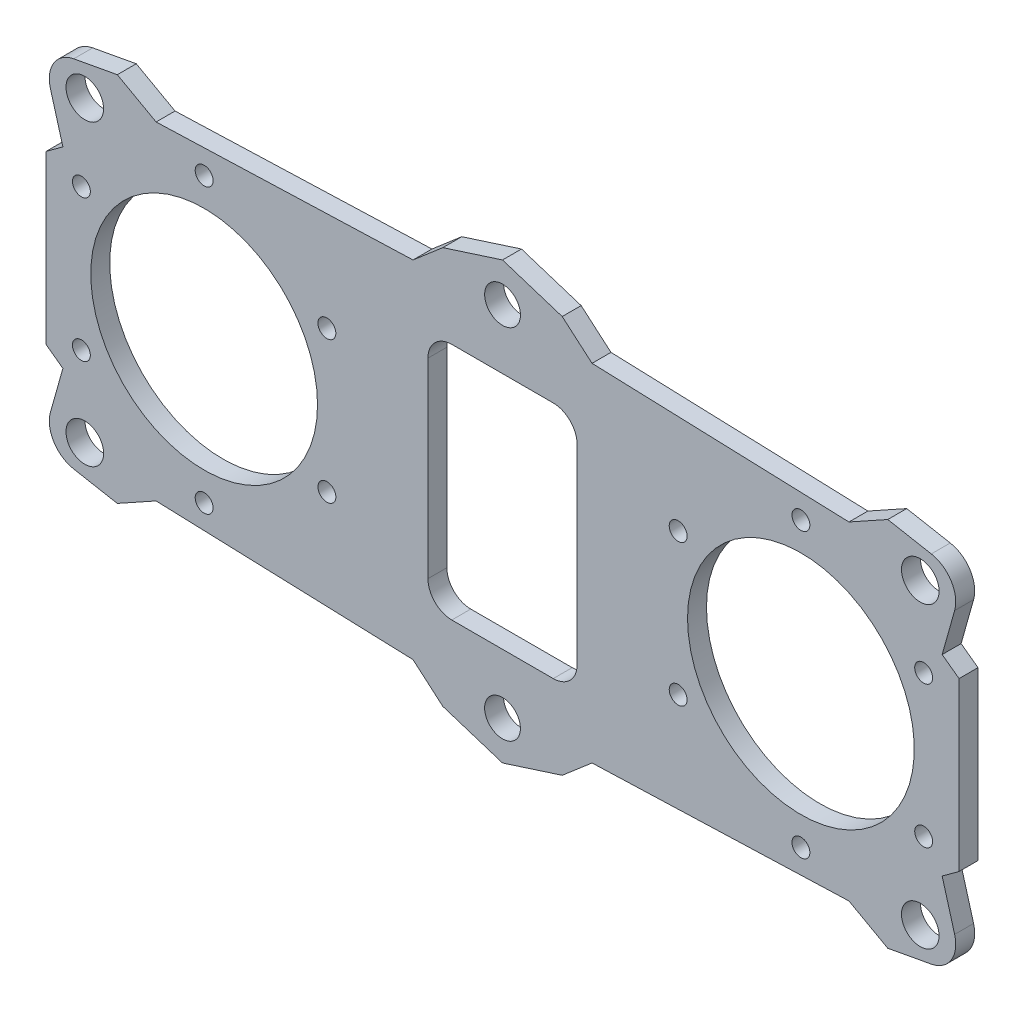
SolidWorks part; units mm, degrees
ref_plane "Front Plane" through (0, 0, 0) normal (0, 0, 1) x (1, 0, 0)
ref_plane "Top Plane" through (0, 0, 0) normal (0, 1, 0) x (1, 0, 0)
ref_plane "Right Plane" through (0, 0, 0) normal (1, 0, 0) x (0, 0, -1)
sketch "Sketch1" plane through (0, 0, 0) normal (0, 0, 1) x (1, 0, 0)
  line L0 (0, 36.5) -> (-10, 33.2896)
  line L1 (-10, 33.2896) -> (-15, 29)
  line L2 (-15, 29) -> (-58.05, 27.5)
  line L3 (-58.05, 27.5) -> (-76.5, 14)
  line L4 (-76.5, 14) -> (-76.5, -14)
  line L5 (-87.0431, 0) -> (20.0163, 0) construction
  line L6 (0, 32.2788) -> (0, 0) construction
  line L7 (76.5, 14) -> (76.5, -14)
  line L8 (58.05, 27.5) -> (76.5, 14)
  line L9 (15, 29) -> (58.05, 27.5)
  line L10 (10, 33.2896) -> (15, 29)
  line L11 (0, 36.5) -> (10, 33.2896)
  line L12 (0, -36.5) -> (10, -33.2896)
  line L13 (10, -33.2896) -> (15, -29)
  line L14 (15, -29) -> (58.05, -27.5)
  line L15 (58.05, -27.5) -> (76.5, -14)
  line L16 (-58.05, -27.5) -> (-76.5, -14)
  line L17 (-15, -29) -> (-58.05, -27.5)
  line L18 (-10, -33.2896) -> (-15, -29)
  line L19 (0, -36.5) -> (-10, -33.2896)
  circle A0 centre (0, 30) radius 3
  circle A1 centre (-50, 0) radius 19
  circle A2 centre (50, 0) radius 19
  circle A3 centre (0, -30) radius 3
  point P35 (76.5, 0)
  point P36 (-76.5, 0)
  dimension "D1" = 6
  dimension "D2" = 38
  dimension "D3" = 60
  dimension "D4" = 100
  dimension "D5" = 153
  dimension "D6" = 73
  dimension "D7" = 28
  dimension "D8" = 55
  dimension "D9" = 18.45
  dimension "D10" = 30
  dimension "D11" = 20
  dimension "D12" = 58
extrude "Boss-Extrude1" add sketch "Sketch1" along normal blind 3.175
sketch "Sketch2" plane through (0, 0, 3.175) normal (0, 0, 1) x (1, 0, 0)
  line L1 (8.5, 20) -> (-8.5, 20)
  line L2 (12.5, 16) -> (12.5, -16)
  line L3 (8.5, -20) -> (-8.5, -20)
  line L4 (-12.5, 16) -> (-12.5, -16)
  line L5 (12.5, 20) -> (-12.5, -20) construction
  line L6 (12.5, -20) -> (-12.5, 20) construction
  arc A1 (8.5, 20) -> (12.5, 16) centre (8.5, 16) cw
  arc A2 (12.5, -16) -> (8.5, -20) centre (8.5, -16) cw
  arc A3 (-8.5, -20) -> (-12.5, -16) centre (-8.5, -16) cw
  arc A4 (-8.5, 20) -> (-12.5, 16) centre (-8.5, 16) ccw
  point P0 (0, 0)
  dimension "D1" = 4
  dimension "D2" = 25
  dimension "D3" = 40
extrude "Cut-Extrude1" cut sketch "Sketch2" against normal through all
sketch "Sketch3" plane through (0, 0, 3.175) normal (0, 0, 1) x (1, 0, 0)
  line L0 (-58.05, 27.5) -> (-64.5519, 31.11)
  line L1 (-58.05, 27.5) -> (-76.5, 14) construction
  line L2 (-64.5519, 31.11) -> (-77.2451, 28.7738)
  line L3 (-77.2451, 28.7738) -> (-73.6694, 16.0712)
  line L4 (-73.6694, 16.0712) -> (-58.05, 27.5)
  line L5 (0, 0) -> (0, 46.5274) construction
  line L6 (73.6694, 16.0712) -> (58.05, 27.5)
  line L7 (77.2451, 28.7738) -> (73.6694, 16.0712)
  line L8 (64.5519, 31.11) -> (77.2451, 28.7738)
  line L9 (58.05, 27.5) -> (64.5519, 31.11)
  line L10 (0, 0) -> (-26.0239, 0) construction
  line L11 (58.05, -27.5) -> (64.5519, -31.11)
  line L12 (64.5519, -31.11) -> (77.2451, -28.7738)
  line L13 (77.2451, -28.7738) -> (73.6694, -16.0712)
  line L14 (73.6694, -16.0712) -> (58.05, -27.5)
  line L15 (-73.6694, -16.0712) -> (-58.05, -27.5)
  line L16 (-77.2451, -28.7738) -> (-73.6694, -16.0712)
  line L17 (-64.5519, -31.11) -> (-77.2451, -28.7738)
  line L18 (-58.05, -27.5) -> (-64.5519, -31.11)
  line L19 (-15, 29) -> (-58.05, 27.5) construction
  circle A0 centre (-70, 25) radius 3.15
  circle A1 centre (70, 25) radius 3.15
  circle A2 centre (-70, -25) radius 3.15
  circle A3 centre (70, -25) radius 3.15
  dimension "D1" = 6.3
  dimension "D2" = 70
  dimension "D3" = 25
extrude "Boss-Extrude2" add sketch "Sketch3" against normal up to surface (3.175 mm away) up to face at (0, 0, 0)
fillet "Fillet1" radius 5 4 edges at (-77.2451, 28.7738, 1.5875) (-77.2451, -28.7738, 1.5875) (77.2451, -28.7738, 1.5875) (77.2451, 28.7738, 1.5875)
sketch "Sketch4" plane through (0, 0, 3.175) normal (0, 0, 1) x (1, 0, 0)
  line L0 (0, 48.5627) -> (0, -47.8194) construction
  circle A0 centre (-50, 0) radius 23.75 construction
  circle A1 centre (-50, 23.75) radius 1.5
  circle A2 centre (-70.5681, 11.875) radius 1.5
  circle A3 centre (-70.5681, -11.875) radius 1.5
  circle A4 centre (-50, -23.75) radius 1.5
  circle A5 centre (-29.4319, -11.875) radius 1.5
  circle A6 centre (-29.4319, 11.875) radius 1.5
  circle A7 centre (29.4319, 11.875) radius 1.5
  circle A8 centre (29.4319, -11.875) radius 1.5
  circle A9 centre (50, -23.75) radius 1.5
  circle A10 centre (70.5681, -11.875) radius 1.5
  circle A11 centre (70.5681, 11.875) radius 1.5
  circle A12 centre (50, 23.75) radius 1.5
  point P21 (-50, 0)
  point P31 (50, 0)
  dimension "D1" = 47.5
  dimension "D3" = 3
  dimension "D2" = 6
extrude "Cut-Extrude2" cut sketch "Sketch4" against normal through all
